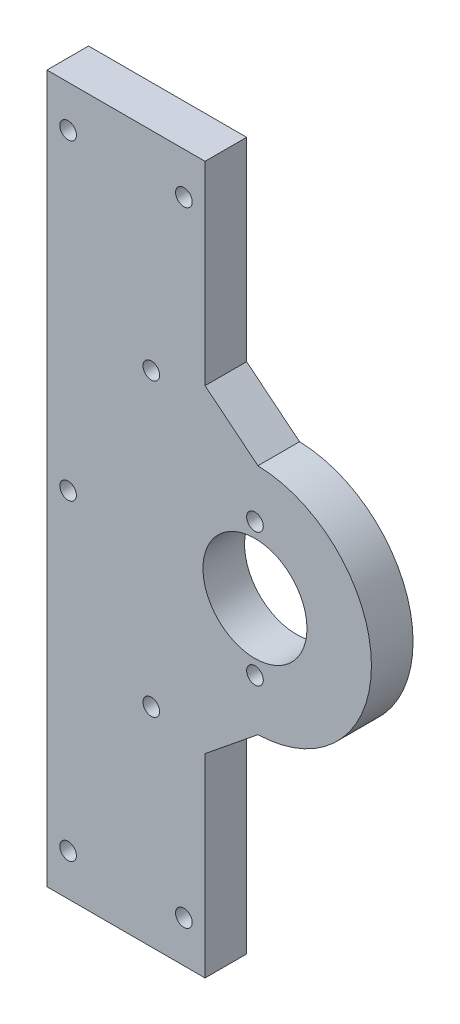
SolidWorks part; units mm, degrees
ref_plane "Front Plane" through (0, 0, 0) normal (0, 0, 1) x (1, 0, 0)
ref_plane "Top Plane" through (0, 0, 0) normal (0, 1, 0) x (1, 0, 0)
ref_plane "Right Plane" through (0, 0, 0) normal (1, 0, 0) x (0, 0, -1)
sketch "Sketch1" plane through (0, 0, 0) normal (0, 0, 1) x (1, 0, 0)
  line L0 (-1, -38.2979) -> (11.7181, -27.9905)
  line L1 (11.7181, 27.9911) -> (-1, 38.2985)
  line L2 (-1, 38.2985) -> (-1, 85)
  line L3 (-1, 85) -> (-39, 85)
  line L4 (-39, 85) -> (-39, -85)
  line L5 (-39, -85) -> (-1, -85)
  line L6 (-1, -85) -> (-1, -38.2979)
  circle A0 centre (-13.9163, -35) radius 2
  circle A1 centre (-13.9163, 35) radius 2
  circle A2 centre (11, 0.0003) radius 12.5
  circle A3 centre (-6.0838, 75) radius 2
  circle A4 centre (-6.0838, -75) radius 2
  circle A5 centre (-33.9163, 75) radius 2
  circle A6 centre (-33.9163, 0) radius 2
  circle A7 centre (11, -15.9997) radius 2
  circle A8 centre (11, 16.0003) radius 2
  circle A9 centre (-33.9163, -75) radius 2
  arc A10 (11.7181, -27.9905) -> (11.7181, 27.9911) centre (11, 0.0003) ccw
  dimension "D1" = 4
  dimension "D2" = 25
  dimension "D3" = 28
  dimension "D4" = 11
  dimension "D5" = 11.7181
  dimension "D6" = 1
  dimension "D7" = 6.0838
  dimension "D8" = 13.9163
  dimension "D9" = 33.9163
  dimension "D10" = 39
  dimension "D11" = 0.0003
  dimension "D12" = 16.0003
  dimension "D13" = 38.2985
  dimension "D14" = 35
  dimension "D15" = 15.9997
  dimension "D16" = 75
  dimension "D17" = 85
  dimension "D20" = 35
  dimension "D22" = 75
  dimension "D23" = 85
extrude "Boss-Extrude1" add sketch "Sketch1" along normal blind 10
